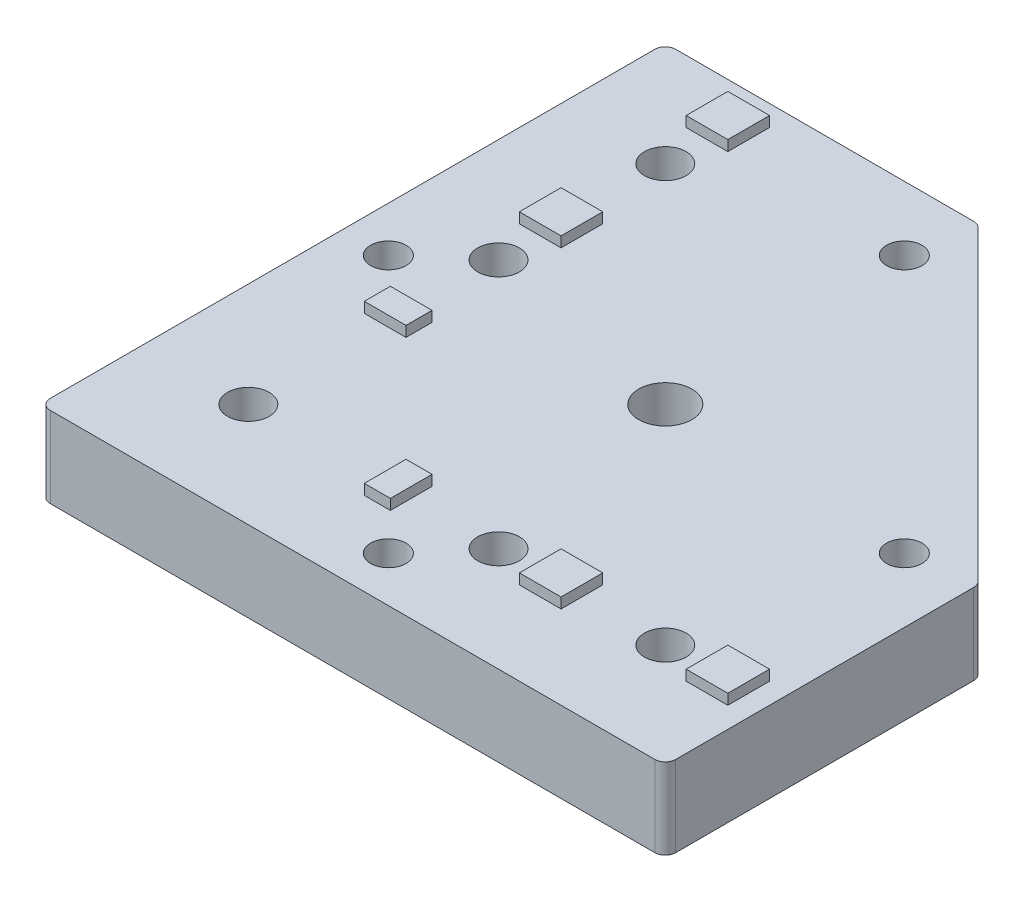
SolidWorks part; units mm, degrees
material "Алюминиевый сплав"
ref_plane "Спереди" through (0, 0, 0) normal (0, 0, 1) x (1, 0, 0)
ref_plane "Сверху" through (0, 0, 0) normal (0, 1, 0) x (1, 0, 0)
ref_plane "Справа" through (0, 0, 0) normal (1, 0, 0) x (0, 0, -1)
sketch "Эскиз1" plane through (0, 0, 0) normal (0, 1, 0) x (1, 0, 0)
  line L0 (0, 0) -> (0, 120)
  line L1 (0, 120) -> (60, 120)
  line L2 (60, 120) -> (120, 60)
  line L3 (120, 60) -> (120, 0)
  line L4 (120, 0) -> (0, 0)
  dimension "D1" = 120
  dimension "D2" = 60
extrude "Бобышка-Вытянуть1" add sketch "Эскиз1" along normal blind 15.5
hole_wizard "Отверстие обработанное метчиком M121" positions "Эскиз2" profile "Эскиз3" tap size "M12" standard "ISO" end condition up to next
sketch "Эскиз2" plane through (0, 15.5, 0) normal (0, 1, 0) x (1, 0, 0)
  line L0 (0, 0) -> (120, 0) construction
  line L2 (120, 0) -> (120, 60) construction
  point P0 (60, 60)
  dimension "D1" = 60
  dimension "D2" = 60
sketch "Эскиз3" plane through (60, 15.5, -60) normal (1, 0, 0) x (0, 0, 1)
  line L0 (0, 0) -> (0, 15.5)
  line L1 (0, 15.5) -> (5.1, 15.5)
  line L2 (5.1, 15.5) -> (5.1, 0)
  line L5 (5.1, 0) -> (0, 0)
  line L11 (0, -6.35) -> (0, 107.95) construction
  dimension "Диаметр проходного сверла" = 10.2
  dimension "Глубина проходного сверла" = 15.5
cosmetic thread "Отверстие резьбы1" parameters "D2"=12
hole_wizard "Отверстие обработанное метчиком M82" positions "Эскиз4" profile "Эскиз5" tap size "M8" standard "ISO" end condition up to next
sketch "Эскиз4" plane through (0, 15.5, 0) normal (0, 1, 0) x (1, 0, 0)
  line L0 (58.1802, 107.6777) -> (8.6827, 58.1802)
  line L1 (8.6827, 58.1802) -> (58.1802, 8.6827)
  line L2 (58.1802, 8.6827) -> (107.6777, 58.1802)
  line L3 (107.6777, 58.1802) -> (58.1802, 107.6777)
  line L5 (120, 60) -> (60, 120) construction
  line L8 (58.1802, 107.6777) -> (58.1802, 8.6827)
  line L9 (33.4315, 33.4315) -> (0, 0)
  point P0 (58.1802, 107.6777)
  point P2 (107.6777, 58.1802)
  point P4 (58.1802, 8.6827)
  point P6 (8.6827, 58.1802)
  dimension "D1" = 70
  dimension "D2" = 70
  dimension "D3" = 10
sketch "Эскиз5" plane through (58.1802, 15.5, -107.6777) normal (1, 0, 0) x (0, 0, 1)
  line L0 (0, 0) -> (0, 15.5)
  line L1 (0, 15.5) -> (3.4, 15.5)
  line L2 (3.4, 15.5) -> (3.4, 0)
  line L5 (3.4, 0) -> (0, 0)
  line L11 (0, -6.35) -> (0, 107.95) construction
  dimension "Диаметр проходного сверла" = 6.8
  dimension "Глубина проходного сверла" = 15.5
cosmetic thread "Отверстие резьбы2" parameters "D2"=8
cosmetic thread "Отверстие резьбы3" parameters "D2"=8
cosmetic thread "Отверстие резьбы4" parameters "D2"=8
cosmetic thread "Отверстие резьбы5" parameters "D2"=8
hole_wizard "Диаметр отверстия Ø8.0 (8)1" positions "Эскиз6" profile "Эскиз8" hole size "Ø8.0" standard "ISO" end condition up to next
sketch "Эскиз6" plane through (0, 15.5, 0) normal (0, 1, 0) x (1, 0, 0)
  line L0 (100, 20) -> (68, 20)
  line L1 (68, 20) -> (20, 20)
  line L2 (20, 20) -> (20, 68)
  line L3 (20, 68) -> (20, 100)
  line L5 (0, 0) -> (120, 0) construction
  line L6 (0, 120) -> (0, 0) construction
  point P0 (20, 100)
  point P2 (20, 68)
  point P4 (20, 20)
  point P6 (68, 20)
  point P8 (100, 20)
  dimension "D1" = 20
  dimension "D2" = 20
  dimension "D3" = 48
  dimension "D4" = 32
sketch "Эскиз8" plane through (20, 15.5, -100) normal (1, 0, 0) x (0, 0, 1)
  line L0 (0, 0) -> (0, 15.5)
  line L1 (0, 15.5) -> (4, 15.5)
  line L2 (4, 15.5) -> (4, 0)
  line L5 (4, 0) -> (0, 0)
  line L11 (0, -6.35) -> (0, 107.95) construction
  dimension "Диаметр сквозного отверстия" = 8
  dimension "Глубина сквозного отверстия" = 15.5
sketch "Эскиз9" plane through (0, 15.5, 0) normal (0, 1, 0) x (1, 0, 0)
  line L0 (0, 0) -> (90, 90) construction
  line L1 (16, 116) -> (24, 116)
  line L2 (16, 116) -> (16, 108)
  line L3 (16, 108) -> (24, 108)
  line L4 (24, 116) -> (24, 108)
  line L5 (16, 116) -> (24, 108) construction
  line L6 (16, 108) -> (24, 116) construction
  line L7 (16, 84) -> (24, 84)
  line L8 (16, 84) -> (16, 76)
  line L9 (16, 76) -> (24, 76)
  line L10 (24, 84) -> (24, 76)
  line L11 (16, 84) -> (24, 76) construction
  line L12 (16, 76) -> (24, 84) construction
  line L13 (16, 51.25) -> (24, 51.25)
  line L14 (16, 51.25) -> (16, 46.25)
  line L15 (16, 46.25) -> (24, 46.25)
  line L16 (24, 51.25) -> (24, 46.25)
  line L17 (16, 51.25) -> (24, 46.25) construction
  line L18 (16, 46.25) -> (24, 51.25) construction
  line L19 (120, 60) -> (60, 120) construction
  line L20 (20, 112) -> (20, 100) construction
  line L21 (20, 100) -> (20, 80) construction
  line L22 (20, 80) -> (20, 48.75) construction
  line L23 (80, 20) -> (48.75, 20) construction
  line L24 (100, 20) -> (80, 20) construction
  line L25 (112, 20) -> (100, 20) construction
  line L26 (46.25, 16) -> (51.25, 24) construction
  line L27 (51.25, 16) -> (46.25, 24) construction
  line L28 (76, 16) -> (84, 24) construction
  line L29 (84, 16) -> (76, 24) construction
  line L30 (108, 16) -> (116, 24) construction
  line L31 (116, 16) -> (108, 24) construction
  line L32 (51.25, 24) -> (46.25, 24)
  line L33 (46.25, 16) -> (46.25, 24)
  line L34 (51.25, 16) -> (46.25, 16)
  line L35 (51.25, 16) -> (51.25, 24)
  line L36 (84, 24) -> (76, 24)
  line L37 (76, 16) -> (76, 24)
  line L38 (84, 16) -> (76, 16)
  line L39 (84, 16) -> (84, 24)
  line L40 (116, 24) -> (108, 24)
  line L41 (108, 16) -> (108, 24)
  line L42 (116, 16) -> (108, 16)
  line L43 (116, 16) -> (116, 24)
  line L44 (60, 120) -> (0, 120) construction
  point P0 (20, 112)
  point P5 (20, 80)
  point P10 (20, 48.75)
  point P51 (48.75, 20)
  point P52 (80, 20)
  point P53 (112, 20)
  dimension "D5" = 24.75
  dimension "D1" = 8
  dimension "D2" = 24
  dimension "D3" = 4
  dimension "D4" = 5
extrude "Бобышка-Вытянуть2" add sketch "Эскиз9" along normal blind 2
fillet "Скругление1" radius 2 5 edges at (0, 7.75, -120) (0, 7.75, 0) (120, 7.75, 0) (120, 7.75, -60) (60, 7.75, -120)
